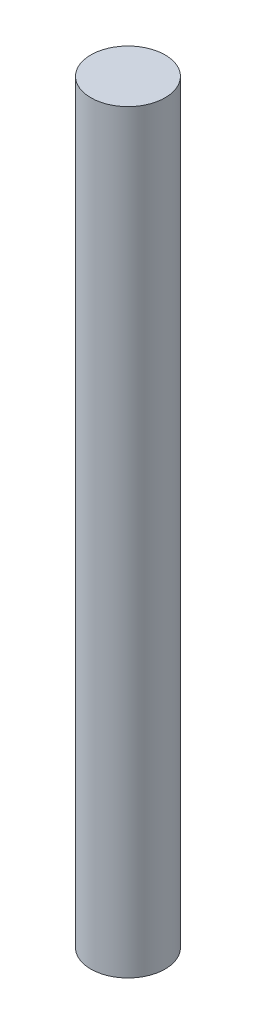
SolidWorks part; units mm, degrees
material "ABS"
ref_plane "Front Plane" through (0, 0, 0) normal (0, 0, 1) x (1, 0, 0)
ref_plane "Top Plane" through (0, 0, 0) normal (0, 1, 0) x (1, 0, 0)
ref_plane "Right Plane" through (0, 0, 0) normal (1, 0, 0) x (0, 0, -1)
sketch "Sketch1" plane through (0, 0, 0) normal (0, 1, 0) x (1, 0, 0)
  circle A0 centre (0, 0) radius 1.25
  dimension "D1" = 2.5
extrude "Boss-Extrude1" add sketch "Sketch1" along normal blind 25.4
